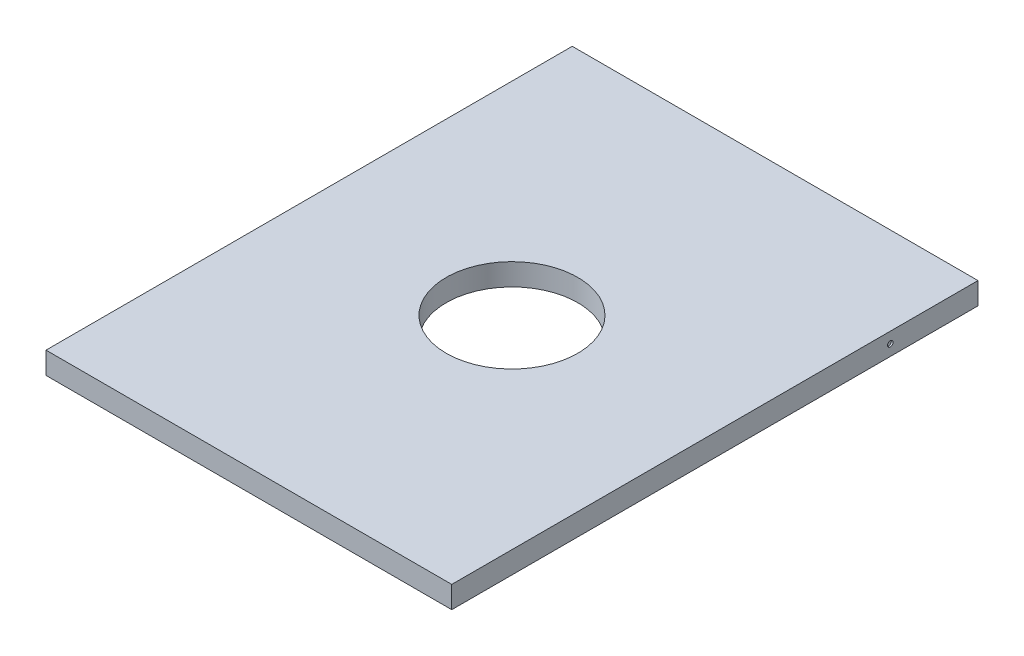
SolidWorks part; units mm, degrees
ref_plane "Front Plane" through (0, 0, 0) normal (0, 0, 1) x (1, 0, 0)
ref_plane "Top Plane" through (0, 0, 0) normal (0, 1, 0) x (1, 0, 0)
ref_plane "Right Plane" through (0, 0, 0) normal (1, 0, 0) x (0, 0, -1)
sketch "Sketch1" plane through (0, 0, 0) normal (0, 1, 0) x (1, 0, 0)
  line L1 (-58.7502, -76.2) -> (58.7502, -76.2)
  line L2 (-58.7502, -76.2) -> (-58.7502, 76.2)
  line L3 (-58.7502, 76.2) -> (58.7502, 76.2)
  line L4 (58.7502, -76.2) -> (58.7502, 76.2)
  line L5 (-58.7502, -76.2) -> (58.7502, 76.2) construction
  line L6 (-58.7502, 76.2) -> (58.7502, -76.2) construction
  circle A0 centre (0, 0) radius 19.05
  point P0 (0, 0)
  dimension "D1" = 152.4
  dimension "D2" = 117.5004
extrude "Boss-Extrude1" add sketch "Sketch1" along normal blind 6.35
sketch "Sketch2" plane through (0, 6.35, 0) normal (0, 1, 0) x (1, 0, 0)
  circle A0 centre (0, 0) radius 19.05
sketch "Sketch3" plane through (-58.7502, 0, 0) normal (-1, 0, 0) x (0, 0, 1)
  line L0 (76.2, 3.175) -> (-76.2, 3.175) construction
  line L1 (76.2, 6.35) -> (76.2, 0) construction
  line L2 (-76.2, 6.35) -> (-76.2, 0) construction
  circle A0 centre (-50.8, 3.175) radius 0.7874
  dimension "D1" = 25.4
extrude "Cut-Extrude1" cut sketch "Sketch3" against normal blind 0.508
sketch "Sketch4" plane through (58.7502, 0, 0) normal (1, 0, 0) x (0, 0, -1)
  line L0 (-76.2, 3.175) -> (76.2, 3.175) construction
  line L1 (-76.2, 6.35) -> (-76.2, 0) construction
  line L2 (76.2, 6.35) -> (76.2, 0) construction
  circle A0 centre (50.8, 3.175) radius 0.7874
  dimension "D1" = 25.4
extrude "Cut-Extrude2" cut sketch "Sketch4" against normal blind 0.508
sketch "Sketch5" plane through (0, 0, -76.2) normal (0, 0, -1) x (-1, 0, 0)
  line L0 (-58.7502, 3.175) -> (58.7502, 3.175) construction
  line L1 (-58.7502, 6.35) -> (-58.7502, 0) construction
  line L2 (58.7502, 6.35) -> (58.7502, 0) construction
  line L4 (-58.7502, 6.35) -> (58.7502, 6.35) construction
  line L5 (0, 6.35) -> (0, 0) construction
  line L6 (-58.7502, 0) -> (58.7502, 0) construction
  circle A0 centre (0, 3.175) radius 1.7272
extrude "Cut-Extrude3" cut sketch "Sketch5" against normal blind 6.35
